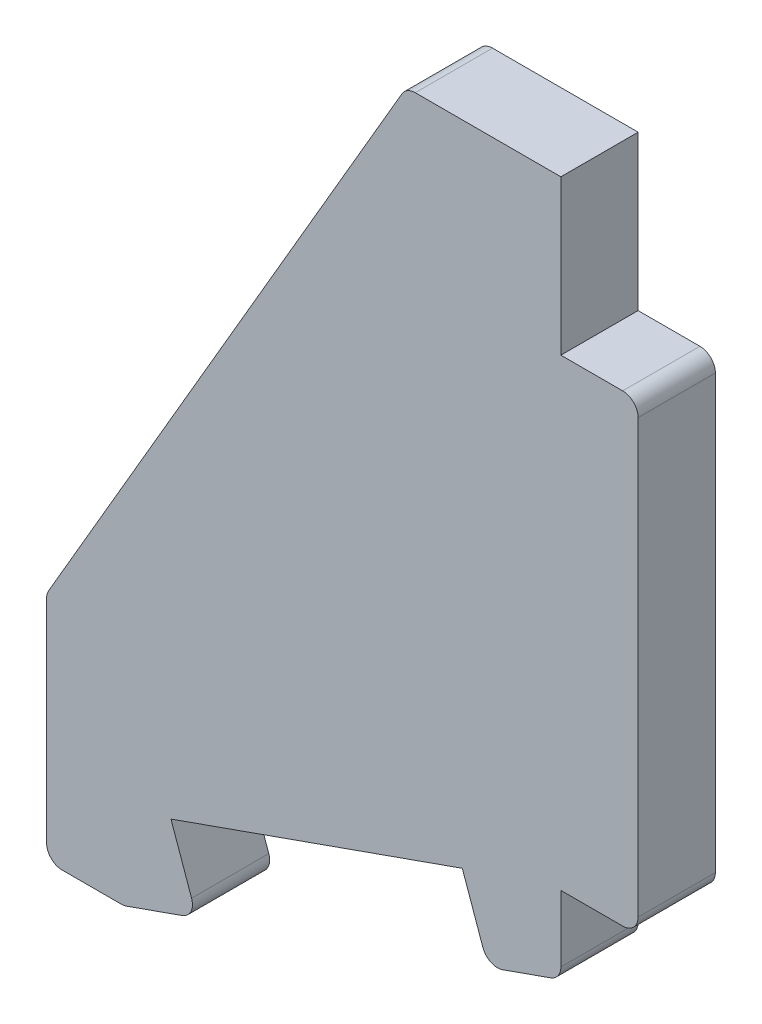
SolidWorks part; units mm, degrees
ref_plane "Front" through (0, 0, 0) normal (0, 0, 1) x (1, 0, 0)
ref_plane "Top" through (0, 0, 0) normal (0, 1, 0) x (1, 0, 0)
ref_plane "Right" through (0, 0, 0) normal (1, 0, 0) x (0, 0, -1)
sketch "Sketch1" plane through (0, 0, 0) normal (0, 0, 1) x (1, 0, 0)
  line L4 (33.2843, 15) -> (33.2843, 45)
  line L6 (28.2843, 10) -> (28.2843, 15)
  line L7 (28.2843, 15) -> (33.2843, 15)
  line L8 (33.2843, 45) -> (28.2843, 45)
  line L9 (28.2843, 45) -> (28.2843, 55)
  line L11 (21.9036, 13.0474) -> (3.0474, 6.3807)
  line L13 (0, 0) -> (-5, 0)
  line L14 (-5, 0) -> (-5, 15)
  line L16 (18.2843, 55) -> (28.2843, 55)
  line L17 (28.2843, 10) -> (23.5702, 8.3333)
  line L18 (23.5702, 8.3333) -> (21.9036, 13.0474)
  line L19 (0, 0) -> (4.714, 1.6667)
  line L20 (4.714, 1.6667) -> (3.0474, 6.3807)
  line L21 (-5, 15) -> (18.2843, 55)
  dimension "D2" = 10
  dimension "D3" = 5
  dimension "D4" = 5
  dimension "D5" = 30
  dimension "D6" = 10
  dimension "D7" = 5
  dimension "D8" = 5
  dimension "D9" = 10
  dimension "D10" = 5
extrude "Boss-Extrude1" add sketch "Sketch1" along normal blind 5
fillet "Fillet1" radius 1 9 edges at (33.2843, 45, 2.5) (33.2843, 15, 2.5) (28.2843, 10, 2.5) (23.5702, 8.3333, 2.5) (4.714, 1.6667, 2.5) (0, 0, 2.5) (-5, 0, 2.5) (-5, 15, 2.5) (18.2843, 55, 2.5)
